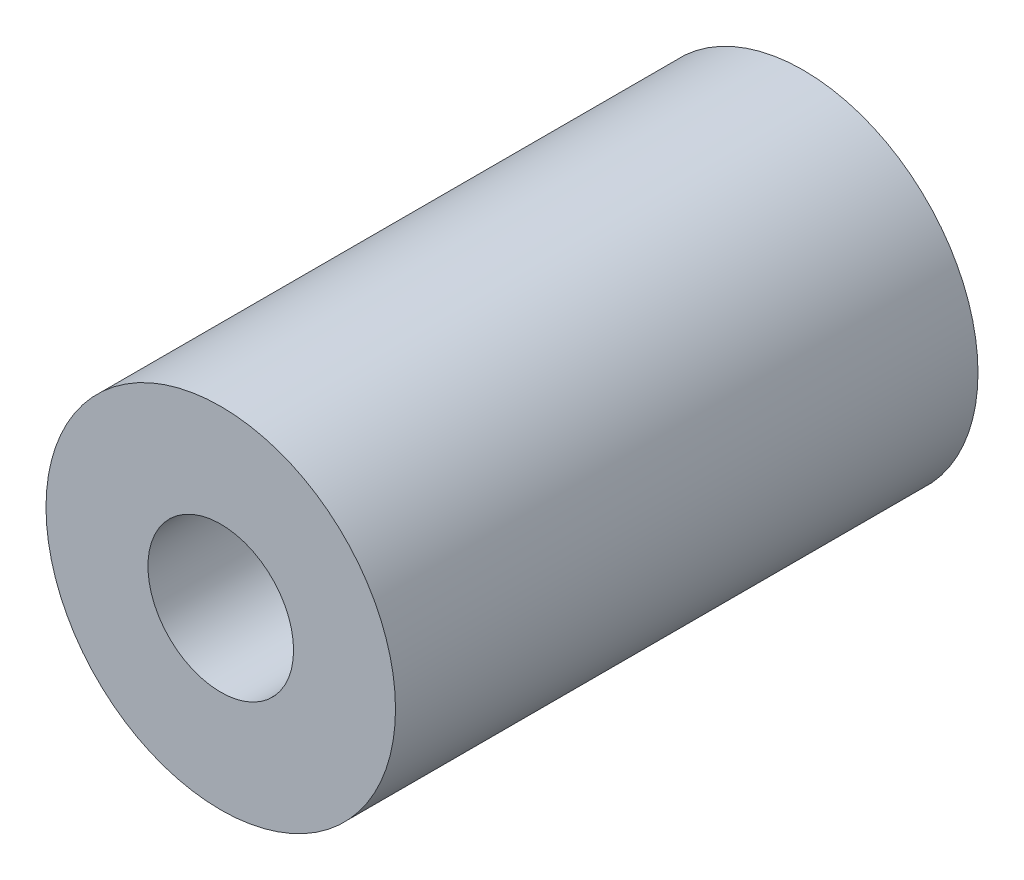
SolidWorks part; units mm, degrees
ref_plane "Front" through (0, 0, 0) normal (0, 0, 1) x (1, 0, 0)
ref_plane "Top" through (0, 0, 0) normal (0, 1, 0) x (1, 0, 0)
ref_plane "Right" through (0, 0, 0) normal (1, 0, 0) x (0, 0, -1)
sketch "Sketch1" plane through (0, 0, 0) normal (0, 0, 1) x (1, 0, 0)
  circle A0 centre (0, 0) radius 3
  dimension "D1" = 6
extrude "Boss-Extrude1" add sketch "Sketch1" along normal blind 10
hole_wizard "M3x0.5 Tapped Hole1" positions "3DSketch2" profile "Sketch3" tap size "M3x0.5" standard "ANSI Metric" end condition through all
sketch3d "3DSketch2"
  line L0 (0, 0, 10) -> (0, 0, 0) construction
  point P0 (0, 0, 10)
sketch "Sketch3" plane through (0, 0, 10) normal (1, 0, 0) x (0, -1, 0)
  line L0 (0, 0) -> (0, 10)
  line L1 (0, 10) -> (1.25, 10)
  line L2 (1.25, 10) -> (1.25, 0)
  line L5 (1.25, 0) -> (0, 0)
  line L11 (0, -6.35) -> (0, 107.95) construction
  dimension "Thru Tap Drill Dia." = 2.5
  dimension "Thru Tap Drill Depth" = 10
cosmetic thread "Hole Thread1" parameters "D2"=3
